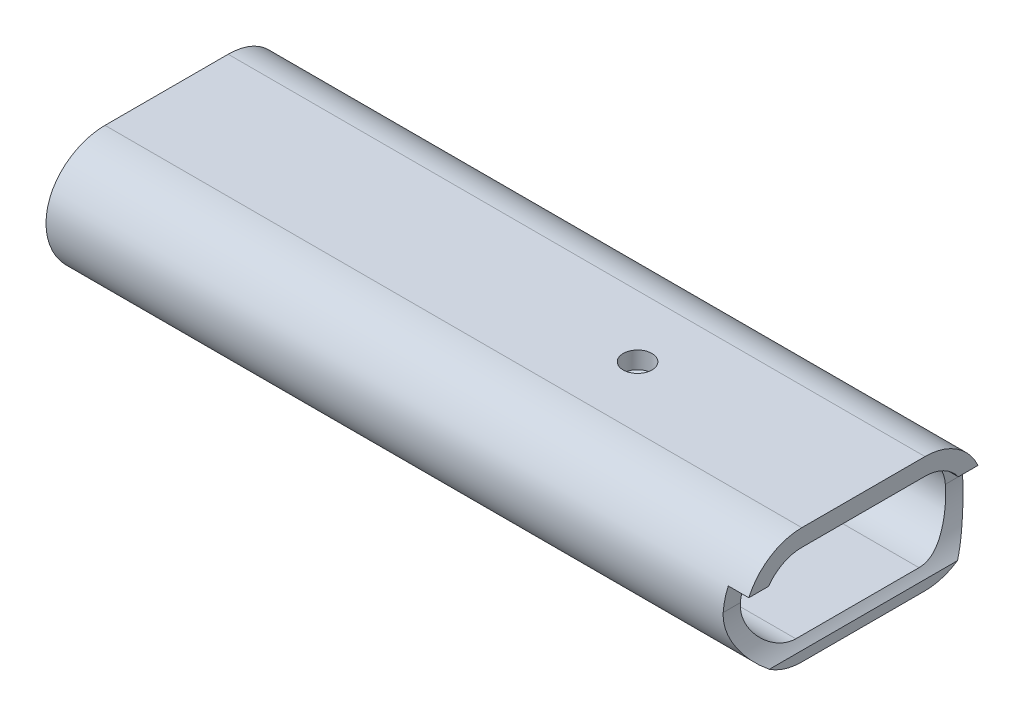
SolidWorks part; units mm, degrees
ref_plane "Plan de face" through (0, 0, 0) normal (0, 0, 1) x (1, 0, 0)
ref_plane "Plan de dessus" through (0, 0, 0) normal (0, 1, 0) x (1, 0, 0)
ref_plane "Plan de droite" through (0, 0, 0) normal (1, 0, 0) x (0, 0, -1)
sketch "Esquisse1" plane through (0, 0, 0) normal (1, 0, 0) x (0, 0, -1)
  line L0 (0, 0) -> (25.7024, 0) construction
  line L1 (-9, -8.5) -> (9, -8.5)
  line L2 (0, 0) -> (0, 31.7948) construction
  line L3 (-9, 8.5) -> (9, 8.5)
  line L4 (-9, 6) -> (9, 6)
  line L5 (-9, -6) -> (9, -6)
  arc A0 (9, 8.5) -> (9, -8.5) centre (9, 0) cw
  arc A1 (-9, 8.5) -> (-9, -8.5) centre (-9, 0) ccw
  arc A2 (9, 6) -> (9, -6) centre (9, 0) cw
  arc A3 (-9, 6) -> (-9, -6) centre (-9, 0) ccw
  dimension "D2" = 35
  dimension "D1" = 17
  dimension "D3" = 2.5
extrude "Extrusion1" add sketch "Esquisse1" along normal mid plane 102
sketch "Esquisse3" plane through (0, 0, 0) normal (0, 0, 1) x (1, 0, 0)
  line L0 (51, 3.5) -> (48, 3.5)
  line L1 (51, -8.5) -> (51, 8.5) construction
  line L2 (48, 3.5) -> (48, 0.5)
  line L3 (51, 3.5) -> (51, -7.0498)
  line L4 (51, 8.5) -> (-51, 8.5) construction
  arc A0 (48, 0.5) -> (51, -7.0498) centre (59, 0.5) ccw
  dimension "D3" = 11
  dimension "D1" = 5
  dimension "D2" = 3
  dimension "D4" = 3
extrude "Enlèv. mat.-Extru.2" cut sketch "Esquisse3" against normal through all and the other way through all
sketch "Esquisse4" plane through (0, 8.5, 0) normal (0, 1, 0) x (-1, 0, 0)
  line L0 (-48, 13.8734) -> (-48, 16.746) construction
  circle A0 centre (-18, 0) radius 2.1
  dimension "D1" = 4.2
  dimension "D2" = 30
extrude "Enlèv. mat.-Extru.3" cut sketch "Esquisse4" against normal up to next
sketch "Esquisse5" plane through (0, 0, 0) normal (0, 0, 1) x (1, 0, 0)
  line L0 (51, 8.5) -> (-51, 8.5) construction
  line L1 (-51, 8.5) -> (-51, -8.5) construction
  arc A0 (-41.3247, -35.5) -> (-50.8247, 8.5) centre (31, 3.1411) cw
  dimension "D1" = 82
  dimension "D3" = 44
  dimension "D2" = 9.5
extrude "Enlèv. mat.-Extru.4" cut sketch "Esquisse5" against normal through all and the other way through all
